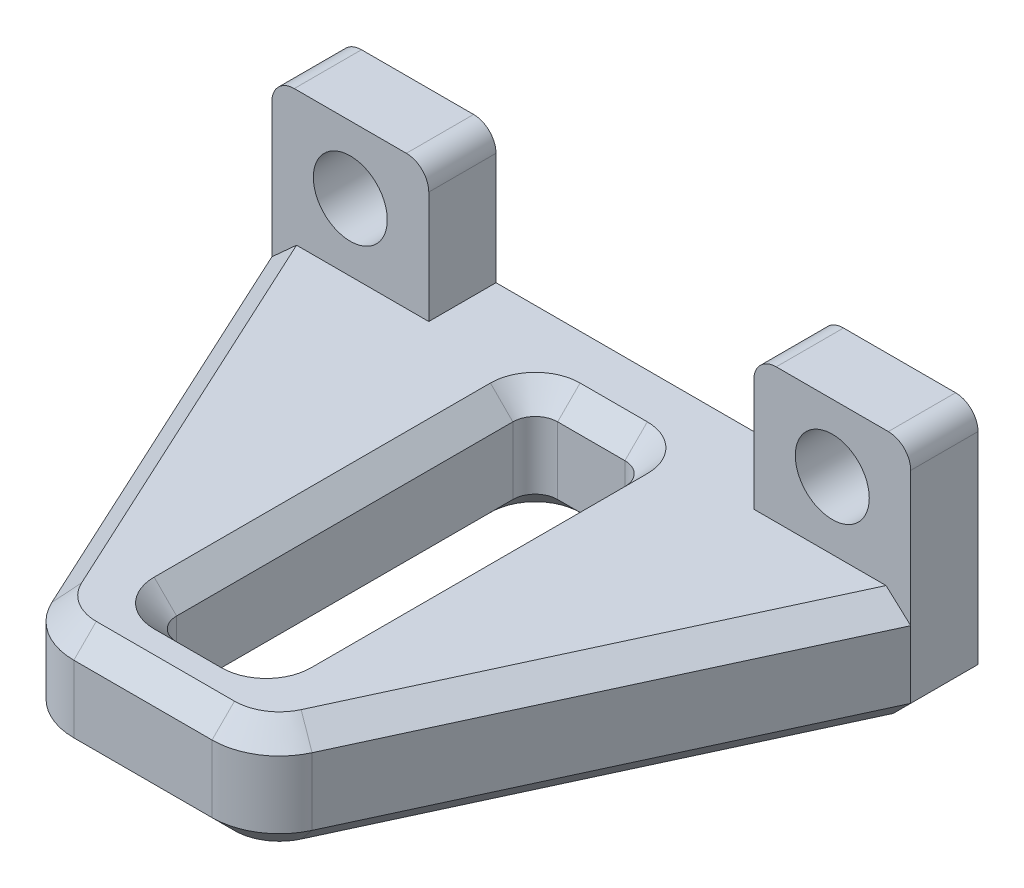
SolidWorks part; units mm, degrees
ref_plane "正面(Front)" through (0, 0, 0) normal (0, 0, 1) x (1, 0, 0)
ref_plane "平面(Top)" through (0, 0, 0) normal (0, 1, 0) x (1, 0, 0)
ref_plane "右側面(Right)" through (0, 0, 0) normal (1, 0, 0) x (0, 0, -1)
sketch "ｽｹｯﾁ1" plane through (0, 0, 0) normal (0, 0, 1) x (1, 0, 0)
  line L0 (0, 0) -> (0, 8.497) construction
  line L1 (0, 0) -> (10.75, 0) construction
  line L2 (-7.25, -3) -> (7.25, -3)
  line L3 (7.25, -3) -> (7.25, 3)
  line L4 (7.25, 3) -> (14.25, 3)
  line L5 (14.25, 3) -> (14.25, -8)
  line L6 (14.25, -8) -> (-14.25, -8)
  line L7 (10.75, 3) -> (10.75, 11.7797) construction
  line L8 (-14.25, 3) -> (-14.25, -8)
  line L9 (-7.25, 3) -> (-14.25, 3)
  line L10 (-7.25, -3) -> (-7.25, 3)
  circle A0 centre (10.75, 0) radius 1.65
  circle A1 centre (-10.75, 0) radius 1.65
  point P12 (0, -8)
  point P17 (0, -3)
  dimension "D1" = 3.3
  dimension "D2" = 21.5
  dimension "D3" = 7
  dimension "D4" = 3
  dimension "D5" = 5
  dimension "D6" = 3
extrude "ﾎﾞｽ - 押し出し1" add sketch "ｽｹｯﾁ1" along normal blind 3
sketch "ｽｹｯﾁ2" plane through (0, -8, 0) normal (0, -1, 0) x (1, 0, 0)
  line L0 (-14.25, 3) -> (-5, 23)
  line L1 (-5, 23) -> (5, 23)
  line L2 (5, 23) -> (14.25, 3)
  line L3 (-14.25, 3) -> (14.25, 3) construction
  line L4 (-14.25, 3) -> (14.25, 3)
  line L5 (0, 0) -> (0, 23.6513) construction
  dimension "D1" = 10
  dimension "D2" = 20
extrude "ﾎﾞｽ - 押し出し2" add sketch "ｽｹｯﾁ2" against normal blind 5
sketch "ｽｹｯﾁ3" plane through (0, -8, 0) normal (0, -1, 0) x (1, 0, 0)
  line L0 (-14.25, 0) -> (14.25, 0) construction
  line L1 (-2.5, 20) -> (2.5, 20)
  line L2 (-2.5, 20) -> (-2.5, 3)
  line L3 (-2.5, 3) -> (2.5, 3)
  line L4 (2.5, 20) -> (2.5, 3)
  line L5 (-2.5, 20) -> (2.5, 3) construction
  line L6 (-2.5, 3) -> (2.5, 20) construction
  line L7 (5, 23) -> (-5, 23) construction
  point P0 (0, 11.5)
  dimension "D1" = 3
  dimension "D2" = 3
  dimension "D3" = 5
extrude "ｶｯﾄ - 押し出し1" cut sketch "ｽｹｯﾁ3" against normal through all
fillet "ﾌｨﾚｯﾄ1" radius 3 2 edges at (-5, -5.5, 23) (5, -5.5, 23)
fillet "ﾌｨﾚｯﾄ2" radius 1 4 edges at (-14.25, 3, 1.5) (-7.25, 3, 1.5) (7.25, 3, 1.5) (14.25, 3, 1.5)
chamfer "面取り1" distance 1 angle 45 12 edges at (-14.25, -8, 1.5) (-10.0275, -8, 12.1297) (-10.0275, -3, 12.1297) (-4.698, -3, 22.5276) (0, -3, 23) (0, -8, 23) (4.698, -3, 22.5276) (10.0275, -3, 12.1297) (10.0275, -8, 12.1297) (-4.698, -8, 22.5276) (4.698, -8, 22.5276) (14.25, -8, 1.5)
fillet "ﾌｨﾚｯﾄ3" radius 1 4 edges at (2.5, -5.5, 3) (-2.5, -5.5, 3) (2.5, -5.5, 20) (-2.5, -5.5, 20)
chamfer "面取り2" distance 1 angle 45 16 edges at (-2.5, -3, 11.5) (-2.2071, -3, 3.2929) (-2.2071, -3, 19.7071) (0, -3, 3) (0, -3, 20) (2.2071, -3, 3.2929) (2.2071, -3, 19.7071) (2.5, -3, 11.5) (-2.5, -8, 11.5) (-2.2071, -8, 3.2929) (-2.2071, -8, 19.7071) (0, -8, 3) (0, -8, 20) (2.2071, -8, 3.2929) (2.2071, -8, 19.7071) (2.5, -8, 11.5)
